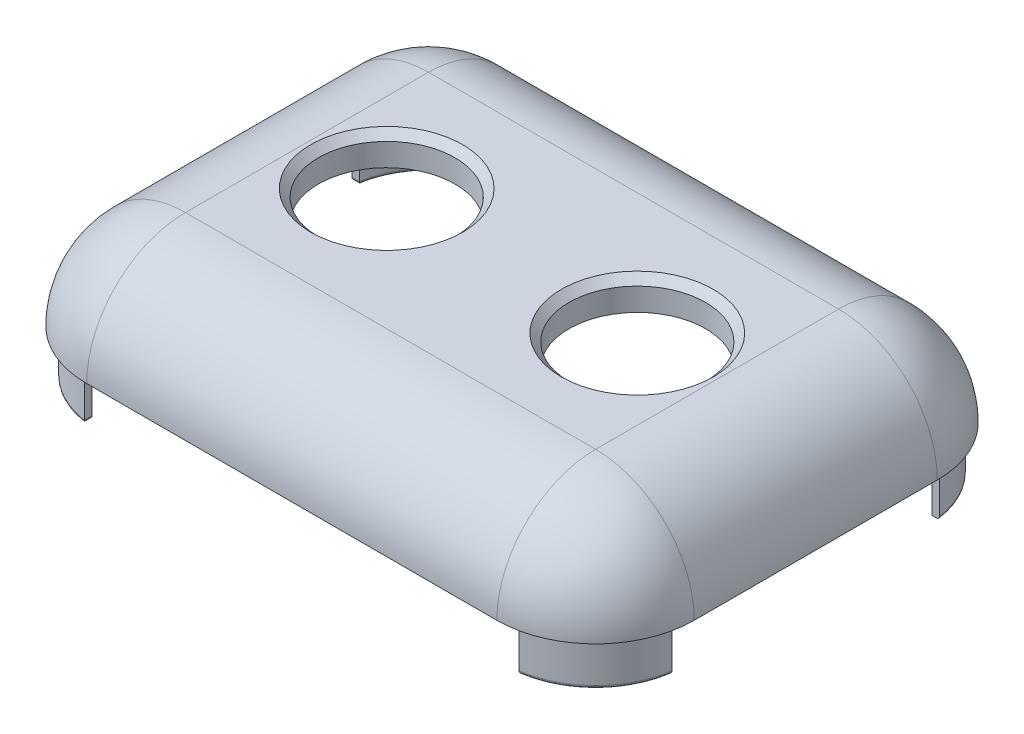
SolidWorks part; units mm, degrees
material "ABS"
ref_plane "Front Plane" through (0, 0, 0) normal (0, 0, 1) x (1, 0, 0)
ref_plane "Top Plane" through (0, 0, 0) normal (0, 1, 0) x (1, 0, 0)
ref_plane "Right Plane" through (0, 0, 0) normal (1, 0, 0) x (0, 0, -1)
sketch "Sketch1" plane through (0, 0, 0) normal (0, 1, 0) x (1, 0, 0)
  line L1 (-20, 14.5) -> (20, 14.5)
  line L2 (-20, 14.5) -> (-20, -14.5)
  line L3 (-20, -14.5) -> (20, -14.5)
  line L4 (20, 14.5) -> (20, -14.5)
  line L5 (0, -14.5) -> (0, 14.5) construction
  line L6 (-20, 0) -> (20, 0) construction
  point P0 (0, 0)
  dimension "D1" = 29
  dimension "D2" = 40
extrude "Boss-Extrude1" add sketch "Sketch1" along normal blind 20
fillet "Fillet2" radius 6.5 12 edges at (0, 20, 14.5) (-20, 20, 0) (0, 20, -14.5) (20, 20, 0) (0, 0, -14.5) (-20, 0, 0) (0, 0, 14.5) (20, 0, 0) (20, 10, 14.5) (20, 10, -14.5) (-20, 10, -14.5) (-20, 10, 14.5)
ref_plane "Plane2" through (0, 13.5, 0) normal (0, 1, 0) x (1, 0, 0)
sketch "Sketch3" plane through (0, 13.5, 0) normal (0, 1, 0) x (1, 0, 0)
  line L1 (24.4913, 19.6546) -> (-24.4913, 19.6546)
  line L2 (24.4913, 19.6546) -> (24.4913, -19.6546)
  line L3 (24.4913, -19.6546) -> (-24.4913, -19.6546)
  line L4 (-24.4913, 19.6546) -> (-24.4913, -19.6546)
  line L5 (0, -19.6546) -> (0, 19.6546) construction
  line L6 (24.4913, 0) -> (-24.4913, 0) construction
  point P0 (0, 0)
extrude "Cut-Extrude1" cut sketch "Sketch3" against normal through all
shell "Shell1" thickness 2
sketch "Sketch5" plane through (0, 13.5, 0) normal (0, -1, 0) x (1, 0, 0)
  line L0 (-14.3, 8.8) -> (-14.3, 15.5483) construction
  line L1 (-13.5, 8) -> (-13.5, 12.5) construction
  line L2 (-13.5, 8) -> (-18, 8) construction
  line L3 (-14.3, 8.8) -> (-21.1716, 8.8) construction
  line L4 (-14.3, 13.8455) -> (-14.3, 13.3404)
  line L5 (-19.3455, 8.8) -> (-18.8404, 8.8)
  line L6 (3.575, 0) -> (-3.575, 0) construction
  line L7 (-14.3, -13.8455) -> (-14.3, -13.3404)
  line L8 (19.4, -8) -> (19.4, 8)
  line L9 (13.5, 13.9) -> (-13.5, 13.9)
  line L10 (-19.4, 8) -> (-19.4, -8)
  line L11 (-13.5, -13.9) -> (13.5, -13.9)
  line L12 (-14.3, -8.8) -> (-14.3, -15.5483) construction
  line L13 (-14.3, -8.8) -> (-21.1716, -8.8) construction
  line L14 (-19.3455, -8.8) -> (-18.8404, -8.8)
  line L15 (0, -3.575) -> (0, 3.575) construction
  line L16 (14.3, -13.8455) -> (14.3, -13.3404)
  line L17 (19.3455, -8.8) -> (18.8404, -8.8)
  line L18 (19.3455, 8.8) -> (18.8404, 8.8)
  line L19 (14.3, 13.8455) -> (14.3, 13.3404)
  arc A0 (-13.5, 13.4) -> (-18.9, 8) centre (-13.5, 8) ccw construction
  arc A1 (-13.5, 13.9) -> (-19.4, 8) centre (-13.5, 8) ccw construction
  arc A2 (-19.4, -8) -> (-13.5, -13.9) centre (-13.5, -8) ccw construction
  arc A3 (-18.9, -8) -> (-13.5, -13.4) centre (-13.5, -8) ccw construction
  arc A4 (14.3, -13.3404) -> (18.8404, -8.8) centre (13.5, -8) ccw
  arc A5 (18.8404, 8.8) -> (14.3, 13.3404) centre (13.5, 8) ccw
  arc A6 (-18.8404, -8.8) -> (-14.3, -13.3404) centre (-13.5, -8) ccw
  arc A7 (-14.3, 13.3404) -> (-18.8404, 8.8) centre (-13.5, 8) ccw
  arc A8 (19.4, 8) -> (13.5, 13.9) centre (13.5, 8) ccw
  arc A9 (-13.5, 13.9) -> (-19.4, 8) centre (-13.5, 8) ccw
  arc A10 (-19.4, -8) -> (-13.5, -13.9) centre (-13.5, -8) ccw
  arc A11 (13.5, -13.9) -> (19.4, -8) centre (13.5, -8) ccw
  arc A12 (19.3455, 8.8) -> (14.3, 13.8455) centre (13.5, 8) ccw
  arc A13 (-14.3, 13.8455) -> (-19.3455, 8.8) centre (-13.5, 8) ccw
  arc A14 (-19.3455, -8.8) -> (-14.3, -13.8455) centre (-13.5, -8) ccw
  arc A15 (14.3, -13.8455) -> (19.3455, -8.8) centre (13.5, -8) ccw
  arc A22 (13.5, -13.4) -> (18.9, -8) centre (13.5, -8) ccw construction
  arc A23 (13.5, -13.9) -> (19.4, -8) centre (13.5, -8) ccw construction
  arc A24 (18.9, 8) -> (13.5, 13.4) centre (13.5, 8) ccw construction
  arc A25 (19.4, 8) -> (13.5, 13.9) centre (13.5, 8) ccw construction
  point P23 (-14.3, 13.8455)
  point P26 (-14.3, 13.3404)
  point P28 (-19.3455, 8.8)
  point P29 (-18.8404, 8.8)
  dimension "D3" = 0.8
  dimension "D4" = 0.8
  dimension "D1" = 0.6
  dimension "D2" = 0.5
extrude "Boss-Extrude3" add sketch "Sketch5" along normal blind 3
fillet "Fillet3" radius 0.2 13 edges at (-17.3184, 10.5, 11.8184) (-17.6719, 10.5, 12.1719) (-17.3184, 10.5, -11.8184) (-17.6719, 10.5, -12.1719) (17.3184, 10.5, 11.8184) (17.6719, 10.5, 12.1719) (17.6719, 10.5, -12.1719) (-14.3, 10.5, 13.593) (-19.093, 10.5, 8.8) (-19.093, 10.5, -8.8) (-14.3, 10.5, -13.593) (19.093, 10.5, 8.8) (14.3, 10.5, 13.593)
sketch "Sketch6" plane through (0, 20, 0) normal (0, 1, 0) x (1, 0, 0)
  line L0 (-8.25, 0) -> (8.25, 0) construction
  circle A0 centre (-8.25, 0) radius 4.5
  circle A1 centre (8.25, 0) radius 4.5
  point P9 (44.7522, 21.5635)
  dimension "D1" = 9
  dimension "D5" = 16.5
extrude "Cut-Extrude2" cut sketch "Sketch6" against normal through all
chamfer "Chamfer1" distance 0.5 angle 45 2 edges at (8.25, 20, -4.5) (-8.25, 20, 4.5)
